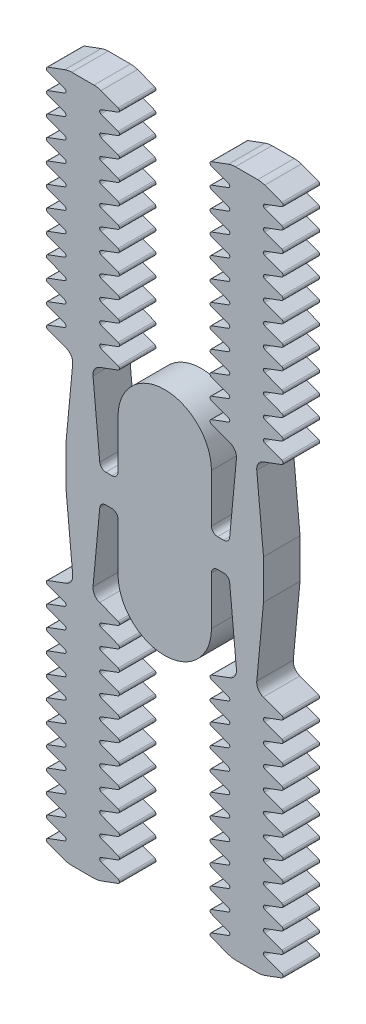
SolidWorks part; units mm, degrees
ref_plane "Front Plane" through (0, 0, 0) normal (0, 0, 1) x (1, 0, 0)
ref_plane "Top Plane" through (0, 0, 0) normal (0, 1, 0) x (1, 0, 0)
ref_plane "Right Plane" through (0, 0, 0) normal (1, 0, 0) x (0, 0, -1)
sketch "Sketch1" plane through (0, 0, 0) normal (0, 0, 1) x (1, 0, 0)
  line L0 (0, 66.02) -> (0, -79.6676) construction
  line L1 (-84.0553, 0) -> (96.3859, 0) construction
  line L2 (23, 33.7413) -> (23, 10)
  line L4 (48.6425, 9.7188) -> (48.6425, -9.7188)
  line L5 (31.3864, 160.415) -> (22.9731, 163.5401)
  line L6 (45.8077, 169.1659) -> (34.8348, 169.1659)
  line L7 (57.6695, 75.415) -> (49.2562, 78.5401)
  line L8 (22.9731, 165.415) -> (31.3864, 168.5401)
  line L9 (31.3864, 150.415) -> (22.9731, 153.5401)
  line L10 (49.2562, 70.415) -> (57.6695, 73.5401)
  line L11 (57.6695, 85.415) -> (49.2562, 88.5401)
  line L12 (22.9731, 155.415) -> (31.3864, 158.5401)
  line L13 (31.3864, 140.415) -> (22.9731, 143.5401)
  line L14 (22.9731, 145.415) -> (31.3864, 148.5401)
  line L15 (31.3864, 130.415) -> (22.9731, 133.5401)
  line L16 (22.9731, 135.415) -> (31.3864, 138.5401)
  line L17 (31.3864, 120.415) -> (22.9731, 123.5401)
  line L18 (22.9731, 125.415) -> (31.3864, 128.5401)
  line L19 (31.3864, 110.415) -> (22.9731, 113.5401)
  line L20 (22.9731, 115.415) -> (31.3864, 118.5401)
  line L21 (31.3864, 100.415) -> (22.9731, 103.5401)
  line L22 (22.9731, 105.415) -> (31.3864, 108.5401)
  line L23 (31.3864, 90.415) -> (22.9731, 93.5401)
  line L24 (22.9731, 95.415) -> (31.3864, 98.5401)
  line L25 (31.3863, 80.415) -> (22.9731, 83.5401)
  line L26 (22.9731, 65.415) -> (31.3863, 68.5401)
  line L27 (31.3863, 60.415) -> (22.9731, 63.5401)
  line L28 (22.9731, 55.415) -> (31.3863, 58.5401)
  line L29 (32.0843, 50.1557) -> (22.9731, 53.5401)
  line L30 (22.9731, 85.415) -> (31.3864, 88.5401)
  line L31 (31.3863, 70.415) -> (22.9731, 73.5401)
  line L32 (22.9731, 75.415) -> (31.3863, 78.5401)
  line L33 (35.3213, 45) -> (32, 9.7188)
  line L34 (26, 7) -> (29.0132, 7)
  line L35 (49.2562, -160.415) -> (57.6695, -163.5401)
  line L36 (57.6695, -165.415) -> (49.2562, -168.5401)
  line L37 (49.2562, -150.415) -> (57.6695, -153.5401)
  line L38 (57.6695, -155.415) -> (49.2562, -158.5401)
  line L39 (49.2562, -140.415) -> (57.6695, -143.5401)
  line L40 (48.5582, 50.1557) -> (57.6695, 53.5401)
  line L41 (57.6695, 55.415) -> (49.2562, 58.5401)
  line L42 (45.3213, 45) -> (48.6425, 9.7188)
  line L43 (49.2562, 60.415) -> (57.6695, 63.5401)
  line L44 (57.6695, 65.415) -> (49.2562, 68.5401)
  line L45 (49.2562, 80.415) -> (57.6695, 83.5401)
  line L46 (40.3213, 210.2412) -> (40.3213, 30.3791) construction
  line L47 (57.6695, 95.415) -> (49.2562, 98.5401)
  line L48 (49.2562, 90.415) -> (57.6695, 93.5401)
  line L49 (57.6695, 105.415) -> (49.2562, 108.5401)
  line L50 (49.2562, 100.415) -> (57.6695, 103.5401)
  line L51 (57.6695, 115.415) -> (49.2562, 118.5401)
  line L52 (49.2562, 110.415) -> (57.6695, 113.5401)
  line L53 (57.6695, 125.415) -> (49.2562, 128.5401)
  line L54 (49.2562, 120.415) -> (57.6695, 123.5401)
  line L55 (57.6695, 135.415) -> (49.2562, 138.5401)
  line L56 (49.2562, 130.415) -> (57.6695, 133.5401)
  line L57 (57.6695, 145.415) -> (49.2562, 148.5401)
  line L58 (49.2562, 140.415) -> (57.6695, 143.5401)
  line L59 (57.6695, 155.415) -> (49.2562, 158.5401)
  line L60 (49.2562, 150.415) -> (57.6695, 153.5401)
  line L61 (57.6695, 165.415) -> (49.2562, 168.5401)
  line L62 (49.2562, 160.415) -> (57.6695, 163.5401)
  line L63 (57.6695, -145.415) -> (49.2562, -148.5401)
  line L64 (49.2562, -130.415) -> (57.6695, -133.5401)
  line L65 (57.6695, -135.415) -> (49.2562, -138.5401)
  line L66 (49.2562, -120.415) -> (57.6695, -123.5401)
  line L67 (57.6695, -125.415) -> (49.2562, -128.5401)
  line L68 (49.2562, -110.415) -> (57.6695, -113.5401)
  line L69 (57.6695, -115.415) -> (49.2562, -118.5401)
  line L70 (49.2562, -100.415) -> (57.6695, -103.5401)
  line L71 (57.6695, -105.415) -> (49.2562, -108.5401)
  line L72 (49.2562, -90.415) -> (57.6695, -93.5401)
  line L73 (57.6695, -95.415) -> (49.2562, -98.5401)
  line L74 (49.2562, -80.415) -> (57.6695, -83.5401)
  line L75 (57.6695, -65.415) -> (49.2562, -68.5401)
  line L76 (49.2562, -60.415) -> (57.6695, -63.5401)
  line L77 (45.3213, -45) -> (48.6425, -9.7188)
  line L78 (57.6695, -55.415) -> (49.2562, -58.5401)
  line L79 (48.5582, -50.1557) -> (57.6695, -53.5401)
  line L80 (35.3213, -45) -> (32, -9.7188)
  line L81 (22.9731, -75.415) -> (31.3863, -78.5401)
  line L82 (31.3863, -70.415) -> (22.9731, -73.5401)
  line L83 (22.9731, -85.415) -> (31.3864, -88.5401)
  line L84 (32.0843, -50.1557) -> (22.9731, -53.5401)
  line L85 (22.9731, -55.415) -> (31.3863, -58.5401)
  line L86 (31.3863, -60.415) -> (22.9731, -63.5401)
  line L87 (22.9731, -65.415) -> (31.3863, -68.5401)
  line L88 (31.3863, -80.415) -> (22.9731, -83.5401)
  line L89 (22.9731, -95.415) -> (31.3864, -98.5401)
  line L90 (31.3864, -90.415) -> (22.9731, -93.5401)
  line L91 (22.9731, -105.415) -> (31.3864, -108.5401)
  line L92 (31.3864, -100.415) -> (22.9731, -103.5401)
  line L93 (22.9731, -115.415) -> (31.3864, -118.5401)
  line L94 (31.3864, -110.415) -> (22.9731, -113.5401)
  line L95 (22.9731, -125.415) -> (31.3864, -128.5401)
  line L96 (31.3864, -120.415) -> (22.9731, -123.5401)
  line L97 (22.9731, -135.415) -> (31.3864, -138.5401)
  line L98 (31.3864, -130.415) -> (22.9731, -133.5401)
  line L99 (22.9731, -145.415) -> (31.3864, -148.5401)
  line L100 (31.3864, -140.415) -> (22.9731, -143.5401)
  line L101 (22.9731, -155.415) -> (31.3864, -158.5401)
  line L102 (57.6695, -85.415) -> (49.2562, -88.5401)
  line L103 (49.2562, -70.415) -> (57.6695, -73.5401)
  line L104 (31.3864, -150.415) -> (22.9731, -153.5401)
  line L105 (22.9731, -165.415) -> (31.3864, -168.5401)
  line L106 (57.6695, -75.415) -> (49.2562, -78.5401)
  line L107 (45.8077, -169.1659) -> (34.8348, -169.1659)
  line L108 (31.3864, -160.415) -> (22.9731, -163.5401)
  line L110 (23, -33.7413) -> (23, -10)
  line L112 (-23, -33.7413) -> (-23, -10)
  line L113 (-26, -7) -> (-29.0132, -7)
  line L114 (-31.3864, -160.415) -> (-22.9731, -163.5401)
  line L115 (-45.8077, -169.1659) -> (-34.8348, -169.1659)
  line L116 (-57.6695, -75.415) -> (-49.2562, -78.5401)
  line L117 (-22.9731, -165.415) -> (-31.3864, -168.5401)
  line L118 (-31.3864, -150.415) -> (-22.9731, -153.5401)
  line L119 (-49.2562, -70.415) -> (-57.6695, -73.5401)
  line L120 (-57.6695, -85.415) -> (-49.2562, -88.5401)
  line L121 (-22.9731, -155.415) -> (-31.3864, -158.5401)
  line L122 (-31.3864, -140.415) -> (-22.9731, -143.5401)
  line L123 (-22.9731, -145.415) -> (-31.3864, -148.5401)
  line L124 (-31.3864, -130.415) -> (-22.9731, -133.5401)
  line L125 (-22.9731, -135.415) -> (-31.3864, -138.5401)
  line L126 (-31.3864, -120.415) -> (-22.9731, -123.5401)
  line L127 (-22.9731, -125.415) -> (-31.3864, -128.5401)
  line L128 (-31.3864, -110.415) -> (-22.9731, -113.5401)
  line L129 (-22.9731, -115.415) -> (-31.3864, -118.5401)
  line L130 (-31.3864, -100.415) -> (-22.9731, -103.5401)
  line L131 (-22.9731, -105.415) -> (-31.3864, -108.5401)
  line L132 (-31.3864, -90.415) -> (-22.9731, -93.5401)
  line L133 (-22.9731, -95.415) -> (-31.3864, -98.5401)
  line L134 (-31.3863, -80.415) -> (-22.9731, -83.5401)
  line L135 (-22.9731, -65.415) -> (-31.3863, -68.5401)
  line L136 (-31.3863, -60.415) -> (-22.9731, -63.5401)
  line L137 (-22.9731, -55.415) -> (-31.3863, -58.5401)
  line L138 (-32.0843, -50.1557) -> (-22.9731, -53.5401)
  line L139 (-22.9731, -85.415) -> (-31.3864, -88.5401)
  line L140 (-31.3863, -70.415) -> (-22.9731, -73.5401)
  line L141 (-22.9731, -75.415) -> (-31.3863, -78.5401)
  line L142 (-35.3213, -45) -> (-32, -9.7188)
  line L143 (-48.5582, -50.1557) -> (-57.6695, -53.5401)
  line L144 (-57.6695, -55.415) -> (-49.2562, -58.5401)
  line L145 (-45.3213, -45) -> (-48.6425, -9.7188)
  line L146 (-49.2562, -60.415) -> (-57.6695, -63.5401)
  line L147 (-57.6695, -65.415) -> (-49.2562, -68.5401)
  line L148 (-49.2562, -80.415) -> (-57.6695, -83.5401)
  line L149 (-57.6695, -95.415) -> (-49.2562, -98.5401)
  line L150 (-49.2562, -90.415) -> (-57.6695, -93.5401)
  line L151 (-57.6695, -105.415) -> (-49.2562, -108.5401)
  line L152 (-49.2562, -100.415) -> (-57.6695, -103.5401)
  line L153 (-57.6695, -115.415) -> (-49.2562, -118.5401)
  line L154 (-49.2562, -110.415) -> (-57.6695, -113.5401)
  line L155 (-57.6695, -125.415) -> (-49.2562, -128.5401)
  line L156 (-49.2562, -120.415) -> (-57.6695, -123.5401)
  line L157 (-57.6695, -135.415) -> (-49.2562, -138.5401)
  line L158 (-49.2562, -130.415) -> (-57.6695, -133.5401)
  line L159 (-57.6695, -145.415) -> (-49.2562, -148.5401)
  line L160 (-49.2562, 160.415) -> (-57.6695, 163.5401)
  line L161 (-57.6695, 165.415) -> (-49.2562, 168.5401)
  line L162 (-49.2562, 150.415) -> (-57.6695, 153.5401)
  line L163 (-57.6695, 155.415) -> (-49.2562, 158.5401)
  line L164 (-49.2562, 140.415) -> (-57.6695, 143.5401)
  line L165 (-57.6695, 145.415) -> (-49.2562, 148.5401)
  line L166 (-49.2562, 130.415) -> (-57.6695, 133.5401)
  line L167 (-57.6695, 135.415) -> (-49.2562, 138.5401)
  line L168 (-49.2562, 120.415) -> (-57.6695, 123.5401)
  line L169 (-57.6695, 125.415) -> (-49.2562, 128.5401)
  line L170 (-49.2562, 110.415) -> (-57.6695, 113.5401)
  line L171 (-57.6695, 115.415) -> (-49.2562, 118.5401)
  line L172 (-49.2562, 100.415) -> (-57.6695, 103.5401)
  line L173 (-57.6695, 105.415) -> (-49.2562, 108.5401)
  line L174 (-49.2562, 90.415) -> (-57.6695, 93.5401)
  line L175 (-57.6695, 95.415) -> (-49.2562, 98.5401)
  line L176 (-49.2562, 80.415) -> (-57.6695, 83.5401)
  line L177 (-57.6695, 65.415) -> (-49.2562, 68.5401)
  line L178 (-49.2562, 60.415) -> (-57.6695, 63.5401)
  line L179 (-45.3213, 45) -> (-48.6425, 9.7188)
  line L180 (-57.6695, 55.415) -> (-49.2562, 58.5401)
  line L181 (-48.5582, 50.1557) -> (-57.6695, 53.5401)
  line L182 (-49.2562, -140.415) -> (-57.6695, -143.5401)
  line L183 (-57.6695, -155.415) -> (-49.2562, -158.5401)
  line L184 (-49.2562, -150.415) -> (-57.6695, -153.5401)
  line L185 (-57.6695, -165.415) -> (-49.2562, -168.5401)
  line L186 (-49.2562, -160.415) -> (-57.6695, -163.5401)
  line L188 (-35.3213, 45) -> (-32, 9.7188)
  line L189 (-22.9731, 75.415) -> (-31.3863, 78.5401)
  line L190 (-31.3863, 70.415) -> (-22.9731, 73.5401)
  line L191 (-22.9731, 85.415) -> (-31.3864, 88.5401)
  line L192 (-32.0843, 50.1557) -> (-22.9731, 53.5401)
  line L193 (-22.9731, 55.415) -> (-31.3863, 58.5401)
  line L194 (-31.3863, 60.415) -> (-22.9731, 63.5401)
  line L195 (-22.9731, 65.415) -> (-31.3863, 68.5401)
  line L196 (-31.3863, 80.415) -> (-22.9731, 83.5401)
  line L197 (-22.9731, 95.415) -> (-31.3864, 98.5401)
  line L198 (-31.3864, 90.415) -> (-22.9731, 93.5401)
  line L199 (-22.9731, 105.415) -> (-31.3864, 108.5401)
  line L200 (-31.3864, 100.415) -> (-22.9731, 103.5401)
  line L201 (-22.9731, 115.415) -> (-31.3864, 118.5401)
  line L202 (-31.3864, 110.415) -> (-22.9731, 113.5401)
  line L203 (-22.9731, 125.415) -> (-31.3864, 128.5401)
  line L204 (-31.3864, 120.415) -> (-22.9731, 123.5401)
  line L205 (-22.9731, 135.415) -> (-31.3864, 138.5401)
  line L206 (-31.3864, 130.415) -> (-22.9731, 133.5401)
  line L207 (-22.9731, 145.415) -> (-31.3864, 148.5401)
  line L208 (-31.3864, 140.415) -> (-22.9731, 143.5401)
  line L209 (-22.9731, 155.415) -> (-31.3864, 158.5401)
  line L210 (-57.6695, 85.415) -> (-49.2562, 88.5401)
  line L211 (-49.2562, 70.415) -> (-57.6695, 73.5401)
  line L212 (-31.3864, 150.415) -> (-22.9731, 153.5401)
  line L213 (-22.9731, 165.415) -> (-31.3864, 168.5401)
  line L214 (-57.6695, 75.415) -> (-49.2562, 78.5401)
  line L215 (-45.8077, 169.1659) -> (-34.8348, 169.1659)
  line L216 (-31.3864, 160.415) -> (-22.9731, 163.5401)
  line L217 (-48.6425, 9.7188) -> (-48.6425, -9.7188)
  line L218 (-26, 7) -> (-29.0132, 7)
  line L219 (-23, 33.7413) -> (-23, 10)
  line L266 (26, -7) -> (29.0132, -7)
  arc A0 (23, 33.7413) -> (-23, 33.7413) centre (0, 33.7413) ccw
  arc A3 (49.2562, 168.5401) -> (45.8077, 169.1659) centre (45.7741, 159.166) ccw
  arc A4 (31.3864, 158.5401) -> (31.3864, 160.415) centre (31.0381, 159.4775) ccw
  arc A5 (22.9731, 163.5401) -> (22.9731, 165.415) centre (23.3213, 164.4775) cw
  arc A6 (31.3864, 148.5401) -> (31.3864, 150.415) centre (31.0381, 149.4775) ccw
  arc A7 (22.9731, 153.5401) -> (22.9731, 155.415) centre (23.3213, 154.4775) cw
  arc A8 (31.3864, 138.5401) -> (31.3864, 140.415) centre (31.0381, 139.4775) ccw
  arc A9 (22.9731, 143.5401) -> (22.9731, 145.415) centre (23.3213, 144.4775) cw
  arc A10 (31.3864, 128.5401) -> (31.3864, 130.415) centre (31.0381, 129.4775) ccw
  arc A11 (22.9731, 133.5401) -> (22.9731, 135.415) centre (23.3213, 134.4775) cw
  arc A12 (31.3864, 118.5401) -> (31.3864, 120.415) centre (31.0381, 119.4775) ccw
  arc A13 (22.9731, 123.5401) -> (22.9731, 125.415) centre (23.3213, 124.4775) cw
  arc A14 (31.3864, 108.5401) -> (31.3864, 110.415) centre (31.0381, 109.4775) ccw
  arc A15 (22.9731, 113.5401) -> (22.9731, 115.415) centre (23.3213, 114.4775) cw
  arc A16 (31.3864, 168.5401) -> (34.8348, 169.1659) centre (34.8684, 159.166) cw
  arc A17 (31.3864, 98.5401) -> (31.3864, 100.415) centre (31.0381, 99.4775) ccw
  arc A18 (22.9731, 103.5401) -> (22.9731, 105.415) centre (23.3213, 104.4775) cw
  arc A19 (31.3864, 88.5401) -> (31.3864, 90.415) centre (31.0381, 89.4775) ccw
  arc A20 (22.9731, 93.5401) -> (22.9731, 95.415) centre (23.3213, 94.4775) cw
  arc A21 (31.3863, 78.5401) -> (31.3863, 80.415) centre (31.0381, 79.4775) ccw
  arc A22 (45.3213, 45) -> (48.5582, 50.1557) centre (50.2993, 45.4686) cw
  arc A23 (49.2562, 58.5401) -> (49.2562, 60.415) centre (49.6044, 59.4775) cw
  arc A24 (57.6695, 63.5401) -> (57.6695, 65.415) centre (57.3213, 64.4775) ccw
  arc A25 (57.6695, 53.5401) -> (57.6695, 55.415) centre (57.3213, 54.4775) ccw
  arc A26 (57.6695, 73.5401) -> (57.6695, 75.415) centre (57.3213, 74.4775) ccw
  arc A27 (49.2562, 68.5401) -> (49.2562, 70.415) centre (49.6044, 69.4775) cw
  arc A28 (57.6695, 83.5401) -> (57.6695, 85.415) centre (57.3213, 84.4775) ccw
  arc A29 (49.2562, 78.5401) -> (49.2562, 80.415) centre (49.6044, 79.4775) cw
  arc A30 (57.6695, 93.5401) -> (57.6695, 95.415) centre (57.3213, 94.4775) ccw
  arc A31 (49.2562, 88.5401) -> (49.2562, 90.415) centre (49.6044, 89.4775) cw
  arc A32 (57.6695, 103.5401) -> (57.6695, 105.415) centre (57.3213, 104.4775) ccw
  arc A33 (49.2562, 98.5401) -> (49.2562, 100.415) centre (49.6044, 99.4775) cw
  arc A34 (57.6695, 113.5401) -> (57.6695, 115.415) centre (57.3213, 114.4775) ccw
  arc A35 (49.2562, 108.5401) -> (49.2562, 110.415) centre (49.6044, 109.4775) cw
  arc A36 (57.6695, 123.5401) -> (57.6695, 125.415) centre (57.3213, 124.4775) ccw
  arc A37 (49.2562, 118.5401) -> (49.2562, 120.415) centre (49.6044, 119.4775) cw
  arc A38 (57.6695, 133.5401) -> (57.6695, 135.415) centre (57.3213, 134.4775) ccw
  arc A39 (49.2562, 128.5401) -> (49.2562, 130.415) centre (49.6044, 129.4775) cw
  arc A40 (57.6695, 143.5401) -> (57.6695, 145.415) centre (57.3213, 144.4775) ccw
  arc A41 (49.2562, 138.5401) -> (49.2562, 140.415) centre (49.6044, 139.4775) cw
  arc A42 (57.6695, 153.5401) -> (57.6695, 155.415) centre (57.3213, 154.4775) ccw
  arc A43 (49.2562, 148.5401) -> (49.2562, 150.415) centre (49.6044, 149.4775) cw
  arc A44 (57.6695, 163.5401) -> (57.6695, 165.415) centre (57.3213, 164.4775) ccw
  arc A45 (49.2562, 158.5401) -> (49.2562, 160.415) centre (49.6044, 159.4775) cw
  arc A46 (22.9731, 83.5401) -> (22.9731, 85.415) centre (23.3213, 84.4775) cw
  arc A47 (31.3863, 68.5401) -> (31.3863, 70.415) centre (31.0381, 69.4775) ccw
  arc A48 (22.9731, 73.5401) -> (22.9731, 75.415) centre (23.3213, 74.4775) cw
  arc A49 (22.9731, 53.5401) -> (22.9731, 55.415) centre (23.3213, 54.4775) cw
  arc A50 (22.9731, 63.5401) -> (22.9731, 65.415) centre (23.3213, 64.4775) cw
  arc A51 (31.3863, 58.5401) -> (31.3863, 60.415) centre (31.0381, 59.4775) ccw
  arc A52 (35.3213, 45) -> (32.0843, 50.1557) centre (30.3433, 45.4686) ccw
  arc A53 (26, 7) -> (23, 10) centre (26, 10) cw
  arc A54 (32, 9.7188) -> (29.0132, 7) centre (29.0132, 10) cw
  arc A55 (35.3213, -45) -> (32.0843, -50.1557) centre (30.3433, -45.4686) cw
  arc A56 (31.3863, -58.5401) -> (31.3863, -60.415) centre (31.0381, -59.4775) cw
  arc A57 (22.9731, -63.5401) -> (22.9731, -65.415) centre (23.3213, -64.4775) ccw
  arc A58 (22.9731, -53.5401) -> (22.9731, -55.415) centre (23.3213, -54.4775) ccw
  arc A59 (22.9731, -73.5401) -> (22.9731, -75.415) centre (23.3213, -74.4775) ccw
  arc A60 (31.3863, -68.5401) -> (31.3863, -70.415) centre (31.0381, -69.4775) cw
  arc A61 (22.9731, -83.5401) -> (22.9731, -85.415) centre (23.3213, -84.4775) ccw
  arc A62 (49.2562, -158.5401) -> (49.2562, -160.415) centre (49.6044, -159.4775) ccw
  arc A63 (57.6695, -163.5401) -> (57.6695, -165.415) centre (57.3213, -164.4775) cw
  arc A64 (49.2562, -148.5401) -> (49.2562, -150.415) centre (49.6044, -149.4775) ccw
  arc A65 (57.6695, -153.5401) -> (57.6695, -155.415) centre (57.3213, -154.4775) cw
  arc A66 (49.2562, -138.5401) -> (49.2562, -140.415) centre (49.6044, -139.4775) ccw
  arc A67 (57.6695, -143.5401) -> (57.6695, -145.415) centre (57.3213, -144.4775) cw
  arc A68 (49.2562, -128.5401) -> (49.2562, -130.415) centre (49.6044, -129.4775) ccw
  arc A69 (57.6695, -133.5401) -> (57.6695, -135.415) centre (57.3213, -134.4775) cw
  arc A70 (49.2562, -118.5401) -> (49.2562, -120.415) centre (49.6044, -119.4775) ccw
  arc A71 (57.6695, -123.5401) -> (57.6695, -125.415) centre (57.3213, -124.4775) cw
  arc A72 (49.2562, -108.5401) -> (49.2562, -110.415) centre (49.6044, -109.4775) ccw
  arc A73 (57.6695, -113.5401) -> (57.6695, -115.415) centre (57.3213, -114.4775) cw
  arc A74 (49.2562, -98.5401) -> (49.2562, -100.415) centre (49.6044, -99.4775) ccw
  arc A75 (57.6695, -103.5401) -> (57.6695, -105.415) centre (57.3213, -104.4775) cw
  arc A76 (49.2562, -88.5401) -> (49.2562, -90.415) centre (49.6044, -89.4775) ccw
  arc A77 (57.6695, -93.5401) -> (57.6695, -95.415) centre (57.3213, -94.4775) cw
  arc A78 (49.2562, -78.5401) -> (49.2562, -80.415) centre (49.6044, -79.4775) ccw
  arc A79 (57.6695, -83.5401) -> (57.6695, -85.415) centre (57.3213, -84.4775) cw
  arc A80 (49.2562, -68.5401) -> (49.2562, -70.415) centre (49.6044, -69.4775) ccw
  arc A81 (57.6695, -73.5401) -> (57.6695, -75.415) centre (57.3213, -74.4775) cw
  arc A82 (57.6695, -53.5401) -> (57.6695, -55.415) centre (57.3213, -54.4775) cw
  arc A83 (57.6695, -63.5401) -> (57.6695, -65.415) centre (57.3213, -64.4775) cw
  arc A84 (49.2562, -58.5401) -> (49.2562, -60.415) centre (49.6044, -59.4775) ccw
  arc A85 (45.3213, -45) -> (48.5582, -50.1557) centre (50.2993, -45.4686) ccw
  arc A86 (31.3863, -78.5401) -> (31.3863, -80.415) centre (31.0381, -79.4775) cw
  arc A87 (22.9731, -93.5401) -> (22.9731, -95.415) centre (23.3213, -94.4775) ccw
  arc A88 (31.3864, -88.5401) -> (31.3864, -90.415) centre (31.0381, -89.4775) cw
  arc A89 (22.9731, -103.5401) -> (22.9731, -105.415) centre (23.3213, -104.4775) ccw
  arc A90 (31.3864, -98.5401) -> (31.3864, -100.415) centre (31.0381, -99.4775) cw
  arc A91 (31.3864, -168.5401) -> (34.8348, -169.1659) centre (34.8684, -159.166) ccw
  arc A92 (22.9731, -113.5401) -> (22.9731, -115.415) centre (23.3213, -114.4775) ccw
  arc A93 (31.3864, -108.5401) -> (31.3864, -110.415) centre (31.0381, -109.4775) cw
  arc A94 (22.9731, -123.5401) -> (22.9731, -125.415) centre (23.3213, -124.4775) ccw
  arc A95 (31.3864, -118.5401) -> (31.3864, -120.415) centre (31.0381, -119.4775) cw
  arc A96 (22.9731, -133.5401) -> (22.9731, -135.415) centre (23.3213, -134.4775) ccw
  arc A97 (31.3864, -128.5401) -> (31.3864, -130.415) centre (31.0381, -129.4775) cw
  arc A98 (22.9731, -143.5401) -> (22.9731, -145.415) centre (23.3213, -144.4775) ccw
  arc A99 (31.3864, -138.5401) -> (31.3864, -140.415) centre (31.0381, -139.4775) cw
  arc A100 (22.9731, -153.5401) -> (22.9731, -155.415) centre (23.3213, -154.4775) ccw
  arc A101 (31.3864, -148.5401) -> (31.3864, -150.415) centre (31.0381, -149.4775) cw
  arc A102 (22.9731, -163.5401) -> (22.9731, -165.415) centre (23.3213, -164.4775) ccw
  arc A103 (31.3864, -158.5401) -> (31.3864, -160.415) centre (31.0381, -159.4775) cw
  arc A104 (49.2562, -168.5401) -> (45.8077, -169.1659) centre (45.7741, -159.166) cw
  arc A107 (23, -33.7413) -> (-23, -33.7413) centre (0, -33.7413) cw
  arc A110 (-26, -7) -> (-23, -10) centre (-26, -10) cw
  arc A111 (-32, -9.7188) -> (-29.0132, -7) centre (-29.0132, -10) cw
  arc A112 (-49.2562, -168.5401) -> (-45.8077, -169.1659) centre (-45.7741, -159.166) ccw
  arc A113 (-31.3864, -158.5401) -> (-31.3864, -160.415) centre (-31.0381, -159.4775) ccw
  arc A114 (-22.9731, -163.5401) -> (-22.9731, -165.415) centre (-23.3213, -164.4775) cw
  arc A115 (-31.3864, -148.5401) -> (-31.3864, -150.415) centre (-31.0381, -149.4775) ccw
  arc A116 (-22.9731, -153.5401) -> (-22.9731, -155.415) centre (-23.3213, -154.4775) cw
  arc A117 (-31.3864, -138.5401) -> (-31.3864, -140.415) centre (-31.0381, -139.4775) ccw
  arc A118 (-22.9731, -143.5401) -> (-22.9731, -145.415) centre (-23.3213, -144.4775) cw
  arc A119 (-31.3864, -128.5401) -> (-31.3864, -130.415) centre (-31.0381, -129.4775) ccw
  arc A120 (-22.9731, -133.5401) -> (-22.9731, -135.415) centre (-23.3213, -134.4775) cw
  arc A121 (-31.3864, -118.5401) -> (-31.3864, -120.415) centre (-31.0381, -119.4775) ccw
  arc A122 (-22.9731, -123.5401) -> (-22.9731, -125.415) centre (-23.3213, -124.4775) cw
  arc A123 (-31.3864, -108.5401) -> (-31.3864, -110.415) centre (-31.0381, -109.4775) ccw
  arc A124 (-22.9731, -113.5401) -> (-22.9731, -115.415) centre (-23.3213, -114.4775) cw
  arc A125 (-31.3864, -168.5401) -> (-34.8348, -169.1659) centre (-34.8684, -159.166) cw
  arc A126 (-31.3864, -98.5401) -> (-31.3864, -100.415) centre (-31.0381, -99.4775) ccw
  arc A127 (-22.9731, -103.5401) -> (-22.9731, -105.415) centre (-23.3213, -104.4775) cw
  arc A128 (-31.3864, -88.5401) -> (-31.3864, -90.415) centre (-31.0381, -89.4775) ccw
  arc A129 (-22.9731, -93.5401) -> (-22.9731, -95.415) centre (-23.3213, -94.4775) cw
  arc A130 (-31.3863, -78.5401) -> (-31.3863, -80.415) centre (-31.0381, -79.4775) ccw
  arc A131 (-45.3213, -45) -> (-48.5582, -50.1557) centre (-50.2993, -45.4686) cw
  arc A132 (-49.2562, -58.5401) -> (-49.2562, -60.415) centre (-49.6044, -59.4775) cw
  arc A133 (-57.6695, -63.5401) -> (-57.6695, -65.415) centre (-57.3213, -64.4775) ccw
  arc A134 (-57.6695, -53.5401) -> (-57.6695, -55.415) centre (-57.3213, -54.4775) ccw
  arc A135 (-57.6695, -73.5401) -> (-57.6695, -75.415) centre (-57.3213, -74.4775) ccw
  arc A136 (-49.2562, -68.5401) -> (-49.2562, -70.415) centre (-49.6044, -69.4775) cw
  arc A137 (-57.6695, -83.5401) -> (-57.6695, -85.415) centre (-57.3213, -84.4775) ccw
  arc A138 (-49.2562, -78.5401) -> (-49.2562, -80.415) centre (-49.6044, -79.4775) cw
  arc A139 (-57.6695, -93.5401) -> (-57.6695, -95.415) centre (-57.3213, -94.4775) ccw
  arc A140 (-49.2562, -88.5401) -> (-49.2562, -90.415) centre (-49.6044, -89.4775) cw
  arc A141 (-57.6695, -103.5401) -> (-57.6695, -105.415) centre (-57.3213, -104.4775) ccw
  arc A142 (-49.2562, -98.5401) -> (-49.2562, -100.415) centre (-49.6044, -99.4775) cw
  arc A143 (-57.6695, -113.5401) -> (-57.6695, -115.415) centre (-57.3213, -114.4775) ccw
  arc A144 (-49.2562, -108.5401) -> (-49.2562, -110.415) centre (-49.6044, -109.4775) cw
  arc A145 (-57.6695, -123.5401) -> (-57.6695, -125.415) centre (-57.3213, -124.4775) ccw
  arc A146 (-49.2562, -118.5401) -> (-49.2562, -120.415) centre (-49.6044, -119.4775) cw
  arc A147 (-57.6695, -133.5401) -> (-57.6695, -135.415) centre (-57.3213, -134.4775) ccw
  arc A148 (-49.2562, -128.5401) -> (-49.2562, -130.415) centre (-49.6044, -129.4775) cw
  arc A149 (-57.6695, -143.5401) -> (-57.6695, -145.415) centre (-57.3213, -144.4775) ccw
  arc A150 (-49.2562, -138.5401) -> (-49.2562, -140.415) centre (-49.6044, -139.4775) cw
  arc A151 (-57.6695, -153.5401) -> (-57.6695, -155.415) centre (-57.3213, -154.4775) ccw
  arc A152 (-49.2562, -148.5401) -> (-49.2562, -150.415) centre (-49.6044, -149.4775) cw
  arc A153 (-57.6695, -163.5401) -> (-57.6695, -165.415) centre (-57.3213, -164.4775) ccw
  arc A154 (-49.2562, -158.5401) -> (-49.2562, -160.415) centre (-49.6044, -159.4775) cw
  arc A155 (-22.9731, -83.5401) -> (-22.9731, -85.415) centre (-23.3213, -84.4775) cw
  arc A156 (-31.3863, -68.5401) -> (-31.3863, -70.415) centre (-31.0381, -69.4775) ccw
  arc A157 (-22.9731, -73.5401) -> (-22.9731, -75.415) centre (-23.3213, -74.4775) cw
  arc A158 (-22.9731, -53.5401) -> (-22.9731, -55.415) centre (-23.3213, -54.4775) cw
  arc A159 (-22.9731, -63.5401) -> (-22.9731, -65.415) centre (-23.3213, -64.4775) cw
  arc A160 (-31.3863, -58.5401) -> (-31.3863, -60.415) centre (-31.0381, -59.4775) ccw
  arc A161 (-35.3213, -45) -> (-32.0843, -50.1557) centre (-30.3433, -45.4686) ccw
  arc A164 (-35.3213, 45) -> (-32.0843, 50.1557) centre (-30.3433, 45.4686) cw
  arc A165 (-31.3863, 58.5401) -> (-31.3863, 60.415) centre (-31.0381, 59.4775) cw
  arc A166 (-22.9731, 63.5401) -> (-22.9731, 65.415) centre (-23.3213, 64.4775) ccw
  arc A167 (-22.9731, 53.5401) -> (-22.9731, 55.415) centre (-23.3213, 54.4775) ccw
  arc A168 (-22.9731, 73.5401) -> (-22.9731, 75.415) centre (-23.3213, 74.4775) ccw
  arc A169 (-31.3863, 68.5401) -> (-31.3863, 70.415) centre (-31.0381, 69.4775) cw
  arc A170 (-22.9731, 83.5401) -> (-22.9731, 85.415) centre (-23.3213, 84.4775) ccw
  arc A171 (-49.2562, 158.5401) -> (-49.2562, 160.415) centre (-49.6044, 159.4775) ccw
  arc A172 (-57.6695, 163.5401) -> (-57.6695, 165.415) centre (-57.3213, 164.4775) cw
  arc A173 (-49.2562, 148.5401) -> (-49.2562, 150.415) centre (-49.6044, 149.4775) ccw
  arc A174 (-57.6695, 153.5401) -> (-57.6695, 155.415) centre (-57.3213, 154.4775) cw
  arc A175 (-49.2562, 138.5401) -> (-49.2562, 140.415) centre (-49.6044, 139.4775) ccw
  arc A176 (-57.6695, 143.5401) -> (-57.6695, 145.415) centre (-57.3213, 144.4775) cw
  arc A177 (-49.2562, 128.5401) -> (-49.2562, 130.415) centre (-49.6044, 129.4775) ccw
  arc A178 (-57.6695, 133.5401) -> (-57.6695, 135.415) centre (-57.3213, 134.4775) cw
  arc A179 (-49.2562, 118.5401) -> (-49.2562, 120.415) centre (-49.6044, 119.4775) ccw
  arc A180 (-57.6695, 123.5401) -> (-57.6695, 125.415) centre (-57.3213, 124.4775) cw
  arc A181 (-49.2562, 108.5401) -> (-49.2562, 110.415) centre (-49.6044, 109.4775) ccw
  arc A182 (-57.6695, 113.5401) -> (-57.6695, 115.415) centre (-57.3213, 114.4775) cw
  arc A183 (-49.2562, 98.5401) -> (-49.2562, 100.415) centre (-49.6044, 99.4775) ccw
  arc A184 (-57.6695, 103.5401) -> (-57.6695, 105.415) centre (-57.3213, 104.4775) cw
  arc A185 (-49.2562, 88.5401) -> (-49.2562, 90.415) centre (-49.6044, 89.4775) ccw
  arc A186 (-57.6695, 93.5401) -> (-57.6695, 95.415) centre (-57.3213, 94.4775) cw
  arc A187 (-49.2562, 78.5401) -> (-49.2562, 80.415) centre (-49.6044, 79.4775) ccw
  arc A188 (-57.6695, 83.5401) -> (-57.6695, 85.415) centre (-57.3213, 84.4775) cw
  arc A189 (-49.2562, 68.5401) -> (-49.2562, 70.415) centre (-49.6044, 69.4775) ccw
  arc A190 (-57.6695, 73.5401) -> (-57.6695, 75.415) centre (-57.3213, 74.4775) cw
  arc A191 (-57.6695, 53.5401) -> (-57.6695, 55.415) centre (-57.3213, 54.4775) cw
  arc A192 (-57.6695, 63.5401) -> (-57.6695, 65.415) centre (-57.3213, 64.4775) cw
  arc A193 (-49.2562, 58.5401) -> (-49.2562, 60.415) centre (-49.6044, 59.4775) ccw
  arc A194 (-45.3213, 45) -> (-48.5582, 50.1557) centre (-50.2993, 45.4686) ccw
  arc A195 (-31.3863, 78.5401) -> (-31.3863, 80.415) centre (-31.0381, 79.4775) cw
  arc A196 (-22.9731, 93.5401) -> (-22.9731, 95.415) centre (-23.3213, 94.4775) ccw
  arc A197 (-31.3864, 88.5401) -> (-31.3864, 90.415) centre (-31.0381, 89.4775) cw
  arc A198 (-22.9731, 103.5401) -> (-22.9731, 105.415) centre (-23.3213, 104.4775) ccw
  arc A199 (-31.3864, 98.5401) -> (-31.3864, 100.415) centre (-31.0381, 99.4775) cw
  arc A200 (-31.3864, 168.5401) -> (-34.8348, 169.1659) centre (-34.8684, 159.166) ccw
  arc A201 (-22.9731, 113.5401) -> (-22.9731, 115.415) centre (-23.3213, 114.4775) ccw
  arc A202 (-31.3864, 108.5401) -> (-31.3864, 110.415) centre (-31.0381, 109.4775) cw
  arc A203 (-22.9731, 123.5401) -> (-22.9731, 125.415) centre (-23.3213, 124.4775) ccw
  arc A204 (-31.3864, 118.5401) -> (-31.3864, 120.415) centre (-31.0381, 119.4775) cw
  arc A205 (-22.9731, 133.5401) -> (-22.9731, 135.415) centre (-23.3213, 134.4775) ccw
  arc A206 (-31.3864, 128.5401) -> (-31.3864, 130.415) centre (-31.0381, 129.4775) cw
  arc A207 (-22.9731, 143.5401) -> (-22.9731, 145.415) centre (-23.3213, 144.4775) ccw
  arc A208 (-31.3864, 138.5401) -> (-31.3864, 140.415) centre (-31.0381, 139.4775) cw
  arc A209 (-22.9731, 153.5401) -> (-22.9731, 155.415) centre (-23.3213, 154.4775) ccw
  arc A210 (-31.3864, 148.5401) -> (-31.3864, 150.415) centre (-31.0381, 149.4775) cw
  arc A211 (-22.9731, 163.5401) -> (-22.9731, 165.415) centre (-23.3213, 164.4775) ccw
  arc A212 (-31.3864, 158.5401) -> (-31.3864, 160.415) centre (-31.0381, 159.4775) cw
  arc A213 (-49.2562, 168.5401) -> (-45.8077, 169.1659) centre (-45.7741, 159.166) cw
  arc A214 (-32, 9.7188) -> (-29.0132, 7) centre (-29.0132, 10) ccw
  arc A215 (-26, 7) -> (-23, 10) centre (-26, 10) ccw
  arc A255 (32, -9.7188) -> (29.0132, -7) centre (29.0132, -10) ccw
  arc A256 (26, -7) -> (23, -10) centre (26, -10) ccw
  point P60 (40.3213, 169.1659)
  point P89 (0, 56.7413)
  point P102 (60.1931, 64.4775)
  point P105 (60.1931, 54.4775)
  point P147 (20.4494, 54.4775)
  point P154 (20.4494, 64.4775)
  point P330 (48.6425, 0)
  point P331 (20.4494, -64.4775)
  point P332 (20.4494, -54.4775)
  point P333 (60.1931, -54.4775)
  point P334 (60.1931, -64.4775)
  point P336 (0, -56.7413)
  point P337 (40.3213, -169.1659)
  point P652 (-48.6425, 0)
  point P653 (-40.3213, -169.1659)
  point P654 (0, -56.7413)
  point P656 (-60.1931, -64.4775)
  point P657 (-60.1931, -54.4775)
  point P658 (-20.4494, -54.4775)
  point P659 (-20.4494, -64.4775)
  point P661 (-20.4494, 64.4775)
  point P662 (-20.4494, 54.4775)
  point P663 (-60.1931, 54.4775)
  point P664 (-60.1931, 64.4775)
  point P666 (0, 56.7413)
  point P667 (-40.3213, 169.1659)
  point P811 (48.6425, 0)
  dimension "D3" = 3
  dimension "D4" = 5
  dimension "D5" = 10
  dimension "D6" = 12
  dimension "D8" = 105
  dimension "D13" = 23
  dimension "D18" = 5
  dimension "D21" = 45
  dimension "D20" = 11
  dimension "D7" = 10
  dimension "D19" = 1
  dimension "D9" = 3
  dimension "D10" = 7
  dimension "D15" = 9
  dimension "D23" = 40.3213
extrude "Boss-Extrude1" add sketch "Sketch1" along normal blind 18
